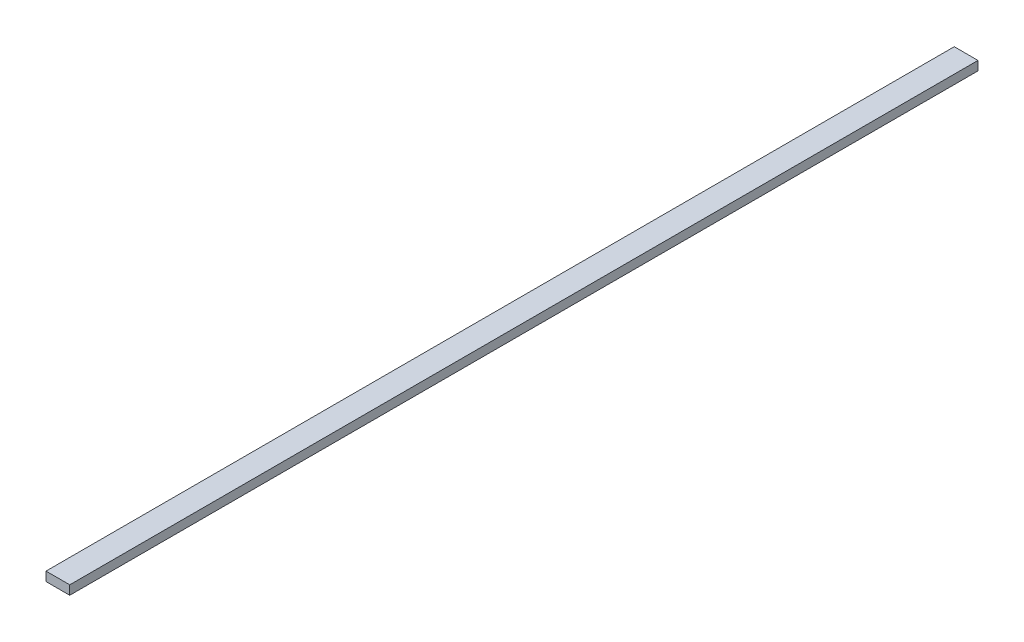
SolidWorks part; units mm, degrees
ref_plane "Front Plane" through (0, 0, 0) normal (0, 0, 1) x (1, 0, 0)
ref_plane "Top Plane" through (0, 0, 0) normal (0, 1, 0) x (1, 0, 0)
ref_plane "Right Plane" through (0, 0, 0) normal (1, 0, 0) x (0, 0, -1)
sketch "Sketch1" plane through (0, 0, 0) normal (0, 0, 1) x (1, 0, 0)
  line L1 (-9.15, -3.5) -> (9.15, -3.5)
  line L2 (-9.15, -3.5) -> (-9.15, 3.5)
  line L3 (-9.15, 3.5) -> (9.15, 3.5)
  line L4 (9.15, -3.5) -> (9.15, 3.5)
  line L5 (-9.15, -3.5) -> (9.15, 3.5) construction
  line L6 (-9.15, 3.5) -> (9.15, -3.5) construction
  point P0 (0, 0)
  dimension "D1" = 18.3
  dimension "D2" = 7
extrude "Boss-Extrude1" add sketch "Sketch1" along normal mid plane 700
